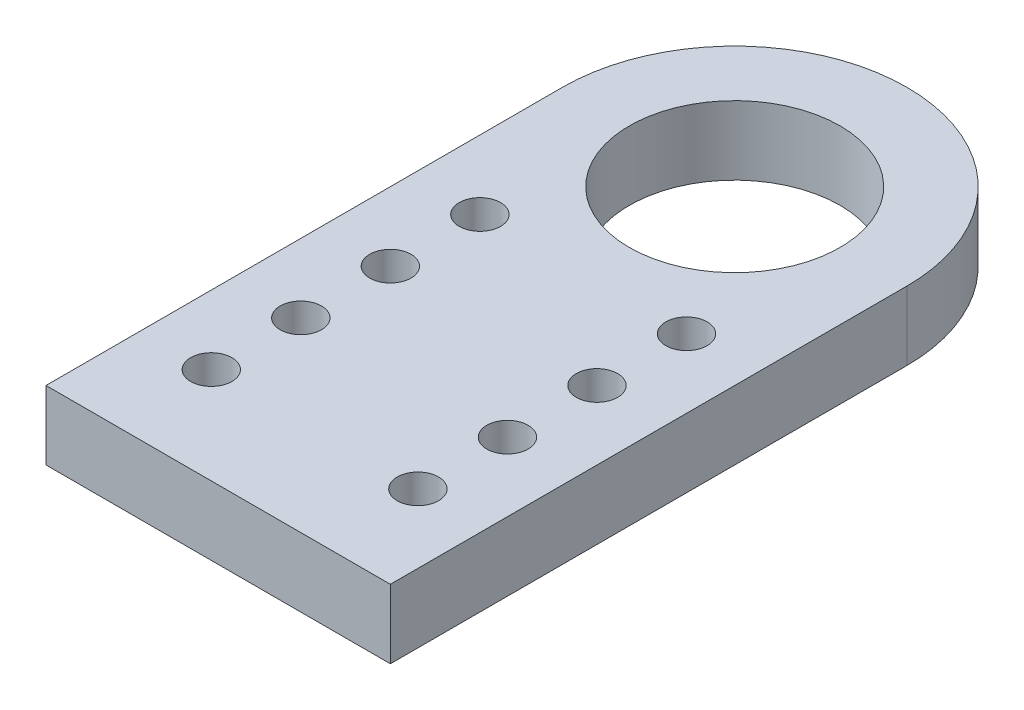
SolidWorks part; units mm, degrees
ref_plane "Спереди" through (0, 0, 0) normal (0, 0, 1) x (1, 0, 0)
ref_plane "Сверху" through (0, 0, 0) normal (0, 1, 0) x (1, 0, 0)
ref_plane "Справа" through (0, 0, 0) normal (1, 0, 0) x (0, 0, -1)
sketch "Эскиз1" plane through (0, 0, 0) normal (0, 1, 0) x (1, 0, 0)
  line L0 (-12.5, 15.8522) -> (-12.5, -21.6478)
  line L1 (-12.5, -21.6478) -> (12.5, -21.6478)
  line L2 (12.5, -21.6478) -> (12.5, 15.8522)
  line L3 (-9, -14.6478) -> (-12.5, -14.6478) construction
  line L4 (9, -14.6478) -> (12.5, -14.6478) construction
  line L5 (-6, -14.6478) -> (6, -14.6478) construction
  line L6 (7.5, -16.1478) -> (7.5, -21.6478) construction
  line L7 (7.5, -13.1478) -> (7.5, -9.6478) construction
  arc A0 (12.5, 15.8522) -> (-12.5, 15.8522) centre (0, 15.8522) ccw
  circle A1 centre (0, 15.8522) radius 7.65
  circle A2 centre (-7.5, -14.6478) radius 1.5
  circle A3 centre (7.5, -14.6478) radius 1.5
  circle A4 centre (-7.5, -8.1478) radius 1.5
  circle A5 centre (7.5, -8.1478) radius 1.5
  circle A6 centre (-7.5, -1.6478) radius 1.5
  circle A7 centre (7.5, -1.6478) radius 1.5
  circle A8 centre (-7.5, 4.8522) radius 1.5
  circle A9 centre (7.5, 4.8522) radius 1.5
  point P5 (0, 28.3522)
  point P6 (0, -21.6478)
  dimension "D1" = 25
  dimension "D3" = 15.3
  dimension "D4" = 3
  dimension "D2" = 50
  dimension "D5" = 12
  dimension "D6" = 5.5
  dimension "D8" = 3.5
  dimension "D7" = 4
extrude "Бобышка-Вытянуть1" add sketch "Эскиз1" along normal blind 5
